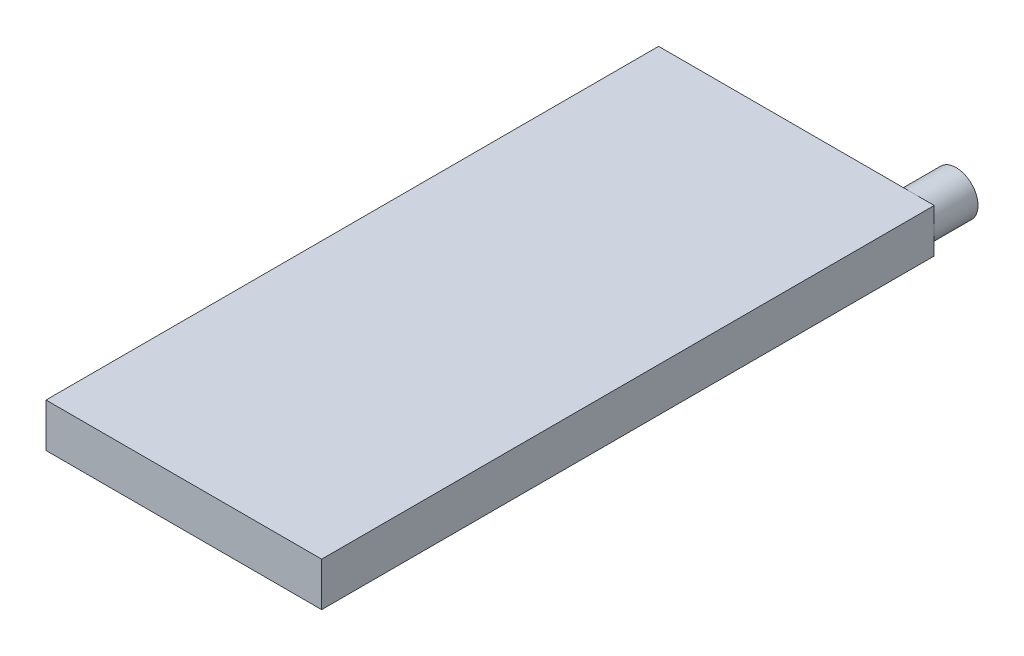
SolidWorks part; units mm, degrees
ref_plane "Plan de face" through (0, 0, 0) normal (0, 0, 1) x (1, 0, 0)
ref_plane "Plan de dessus" through (0, 0, 0) normal (0, 1, 0) x (1, 0, 0)
ref_plane "Plan de droite" through (0, 0, 0) normal (1, 0, 0) x (0, 0, -1)
sketch "Esquisse1" plane through (0, 0, 0) normal (0, 1, 0) x (1, 0, 0)
  line L1 (0, 0) -> (-63, 0)
  line L2 (0, 0) -> (0, 140)
  line L3 (0, 140) -> (-63, 140)
  line L4 (-63, 0) -> (-63, 140)
  dimension "D1" = 140
  dimension "D2" = 63
extrude "Boss.-Extru.1" add sketch "Esquisse1" along normal blind 10
sketch "Esquisse2" plane through (0, 0, -140) normal (0, 0, -1) x (-1, 0, 0)
  line L0 (0, 10) -> (63, 10) construction
  line L1 (0, 10) -> (0, 0) construction
  line L2 (0, 0) -> (63, 0) construction
  circle A0 centre (5, 5) radius 5
extrude "Boss.-Extru.2" add sketch "Esquisse2" along normal blind 10
